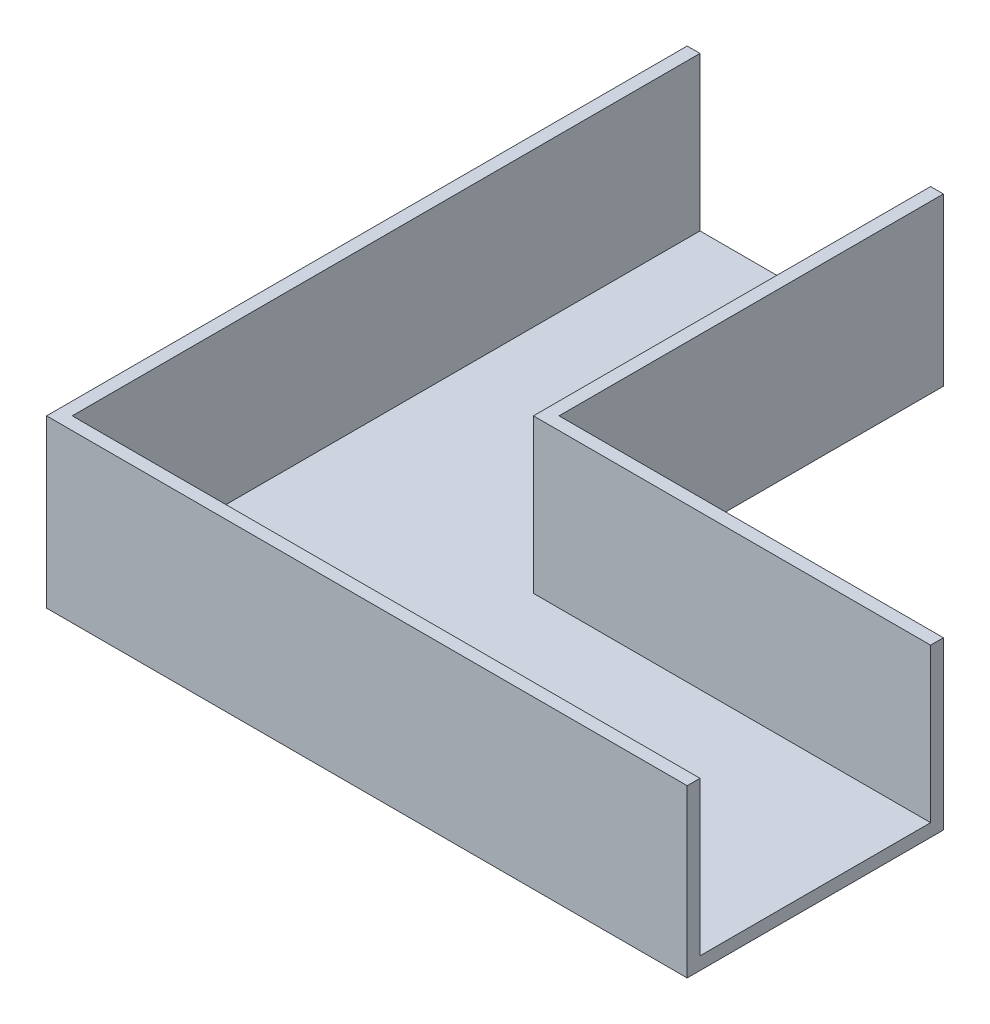
SolidWorks part; units mm, degrees
material "Maple"
ref_plane "Front Plane" through (0, 0, 0) normal (0, 0, 1) x (1, 0, 0)
ref_plane "Top Plane" through (0, 0, 0) normal (0, 1, 0) x (1, 0, 0)
ref_plane "Right Plane" through (0, 0, 0) normal (1, 0, 0) x (0, 0, -1)
sketch "Sketch1" plane through (0, 0, 0) normal (0, 1, 0) x (1, 0, 0)
  line L0 (0, 0) -> (1270, 0)
  line L1 (1270, 0) -> (1270, 508)
  line L2 (1270, 508) -> (508, 508)
  line L3 (508, 508) -> (508, 1270)
  line L4 (508, 1270) -> (0, 1270)
  line L5 (0, 1270) -> (0, 0)
  dimension "D1" = 508
  dimension "D2" = 508
  dimension "D3" = 1270
  dimension "D4" = 1270
extrude "Boss-Extrude1" add sketch "Sketch1" along normal blind 330.2
sketch "Sketch2" plane through (0, 330.2, 0) normal (0, 1, 0) x (1, 0, 0)
  line L0 (25.4, 1270) -> (25.4, 25.4)
  line L1 (508, 1270) -> (0, 1270) construction
  line L2 (25.4, 25.4) -> (1270, 25.4)
  line L3 (1270, 0) -> (1270, 508) construction
  line L4 (1270, 25.4) -> (1270, 482.6)
  line L5 (1270, 482.6) -> (482.6, 482.6)
  line L6 (482.6, 482.6) -> (482.6, 1270)
  line L7 (482.6, 1270) -> (25.4, 1270)
  line L8 (0, 1270) -> (0, 0) construction
  line L9 (508, 508) -> (508, 1270) construction
  line L10 (0, 0) -> (1270, 0) construction
  line L11 (1270, 508) -> (508, 508) construction
  dimension "D1" = 25.4
  dimension "D2" = 25.4
  dimension "D3" = 25.4
  dimension "D4" = 25.4
extrude "Cut-Extrude2" cut sketch "Sketch2" against normal blind 304.8
equation "\"D1@Sketch1\"=18in+2in"
equation "\"D2@Sketch1\"=\"D1@Sketch1\""
equation "\"D3@Sketch1\"=49in+1in"
equation "\"D4@Sketch1\"=\"D3@Sketch1\""
equation "\"D1@Boss-Extrude1\"=12in+1in"
equation "\"D1@Sketch2\"=1in"
equation "\"D2@Sketch2\"=\"D1@Sketch2\""
equation "\"D3@Sketch2\"=\"D1@Sketch2\""
equation "\"D4@Sketch2\"=\"D2@Sketch2\""
equation "\"D1@Cut-Extrude2\"=12in"
